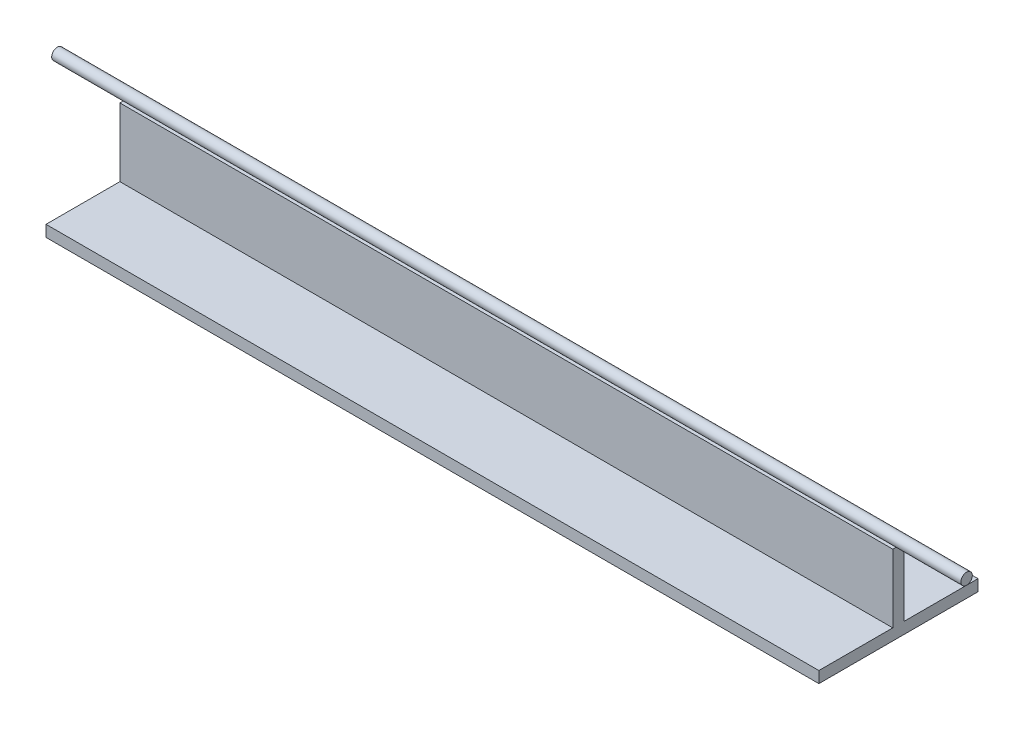
SolidWorks part; units mm, degrees
ref_plane "Front Plane" through (0, 0, 0) normal (0, 0, 1) x (1, 0, 0)
ref_plane "Top Plane" through (0, 0, 0) normal (0, 1, 0) x (1, 0, 0)
ref_plane "Right Plane" through (0, 0, 0) normal (1, 0, 0) x (0, 0, -1)
sketch "Sketch1" plane through (0, 0, 0) normal (0, 1, 0) x (1, 0, 0)
  line L1 (-170, -2.5) -> (170, -2.5)
  line L2 (-170, -2.5) -> (-170, 2.5)
  line L3 (-170, 2.5) -> (170, 2.5)
  line L4 (170, -2.5) -> (170, 2.5)
  line L5 (-170, -2.5) -> (170, 2.5) construction
  line L6 (-170, 2.5) -> (170, -2.5) construction
  point P0 (0, 0)
  dimension "D1" = 340
  dimension "D2" = 5
extrude "Boss-Extrude1" add sketch "Sketch1" along normal blind 30
sketch "Sketch2" plane through (170, 0, 0) normal (1, 0, 0) x (0, 0, -1)
  line L0 (-2.5, 30) -> (2.5, 30) construction
  circle A0 centre (0, 32.5) radius 2.5
  dimension "D2" = 5
  dimension "D1" = 2.5
extrude "Boss-Extrude2" add sketch "Sketch2" along normal blind 30 and the other way blind 370 separate body
sketch "Sketch3" plane through (0, 0, 0) normal (0, -1, 0) x (1, 0, 0)
  line L1 (-170, 35) -> (170, 35)
  line L2 (-170, 35) -> (-170, -35)
  line L3 (-170, -35) -> (170, -35)
  line L4 (170, 35) -> (170, -35)
  line L5 (-170, 35) -> (170, -35) construction
  line L6 (-170, -35) -> (170, 35) construction
  point P0 (0, 0)
  dimension "D1" = 340
  dimension "D2" = 70
extrude "Boss-Extrude3" add sketch "Sketch3" along normal blind 5
